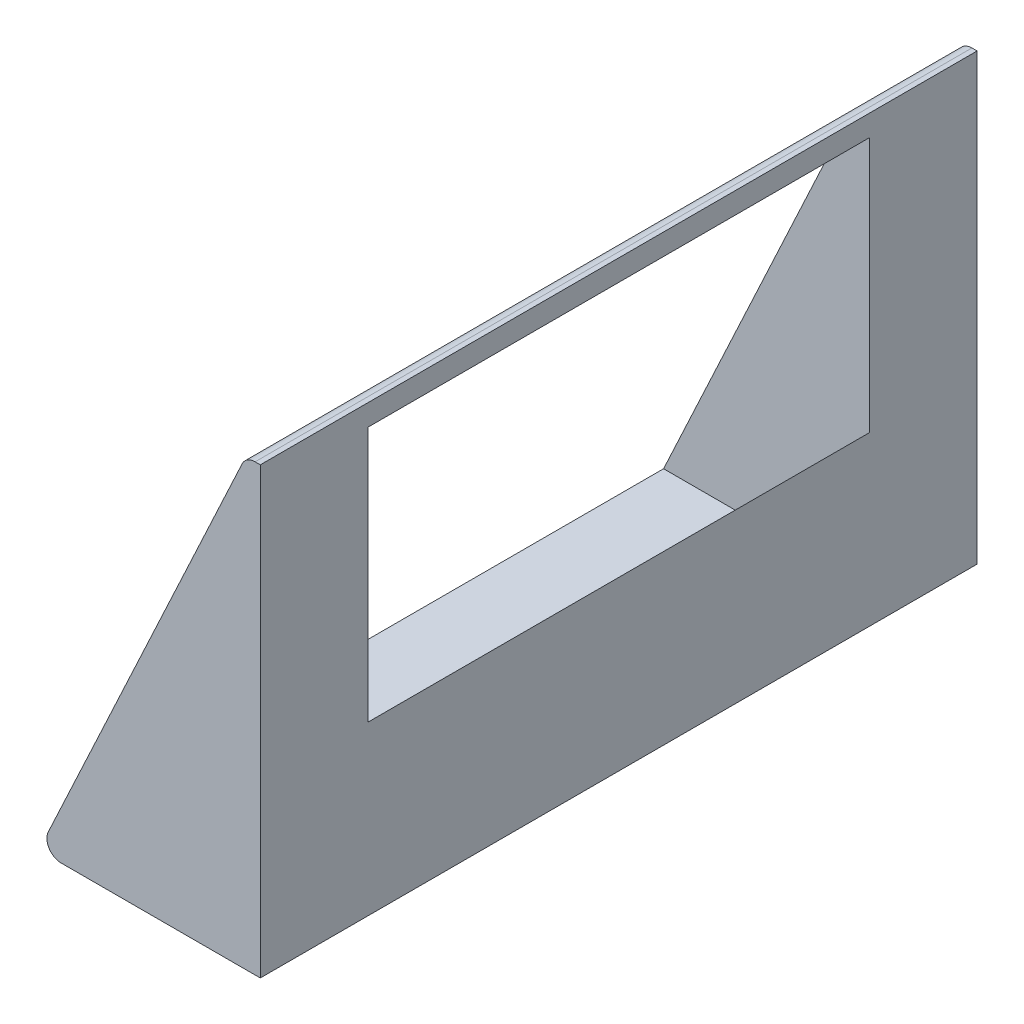
SolidWorks part; units mm, degrees
ref_plane "Front Plane" through (0, 0, 0) normal (0, 0, 1) x (1, 0, 0)
ref_plane "Top Plane" through (0, 0, 0) normal (0, 1, 0) x (1, 0, 0)
ref_plane "Right Plane" through (0, 0, 0) normal (1, 0, 0) x (0, 0, -1)
sketch "Sketch1" plane through (0, 0, 0) normal (0, 0, 1) x (1, 0, 0)
  line L0 (0, 0) -> (0, 310)
  line L1 (0, 310) -> (-3.6293, 310)
  line L2 (-12.6924, 304.2262) -> (-147.9216, 14.2262)
  line L3 (-138.8585, 0) -> (0, 0)
  arc A0 (-3.6293, 310) -> (-12.6924, 304.2262) centre (-3.6293, 300) ccw
  arc A1 (-147.9216, 14.2262) -> (-138.8585, 0) centre (-138.8585, 10) ccw
  point P7 (-10, 310)
  dimension "D4" = 10
  dimension "D1" = 310
  dimension "D2" = 65
  dimension "D3" = 10
extrude "Boss-Extrude1" add sketch "Sketch1" along normal blind 500
sketch "Sketch2" plane through (-126.9508, 59.1981, 0) normal (-0.9063, 0.4226, 0) x (0, 0, 1)
  line L0 (75, 110.3687) -> (0, 110.3687) construction
  line L1 (75, 260.3687) -> (425, 260.3687)
  line L2 (75, 260.3687) -> (75, -39.6313)
  line L3 (75, -39.6313) -> (425, -39.6313)
  line L4 (425, 260.3687) -> (425, -39.6313)
  line L5 (250, -39.6313) -> (250, -65.3179) construction
  line L6 (500, -65.3179) -> (0, -65.3179) construction
  line L7 (0, 270.3585) -> (0, -49.6211) construction
  dimension "D1" = 350
  dimension "D2" = 300
extrude "Cut-Extrude1" cut sketch "Sketch2" along direction (-1, 0, 0) on the side against the normal blind 100
